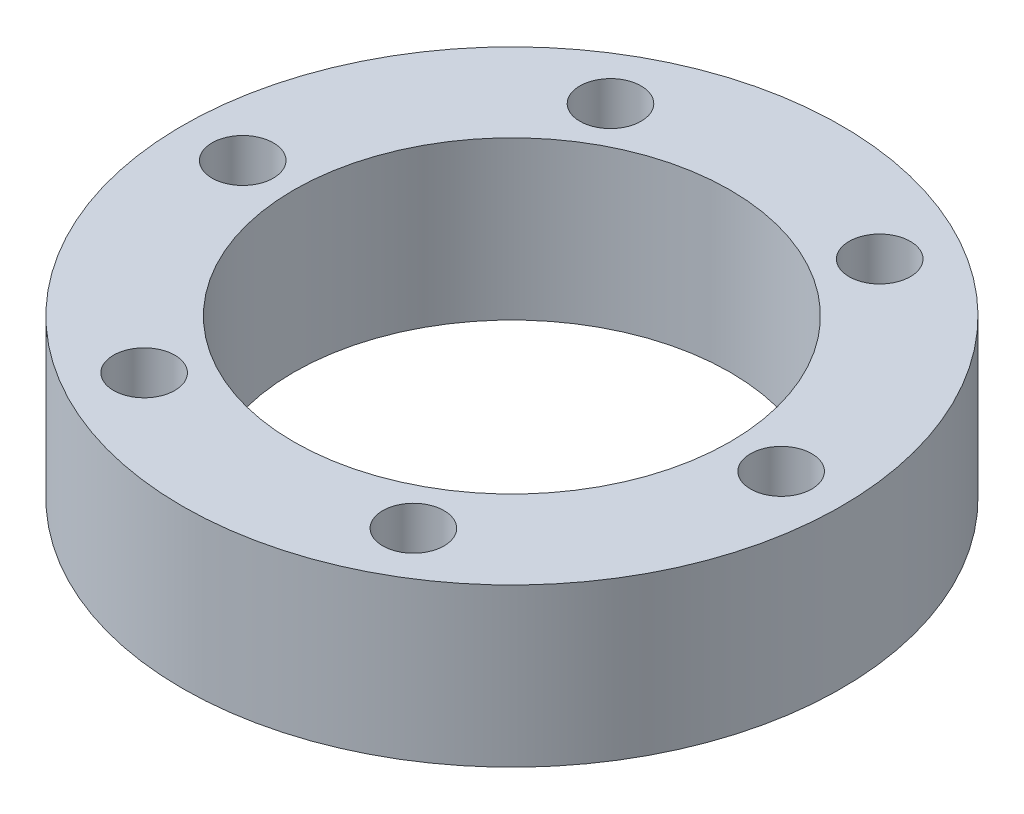
SolidWorks part; units mm, degrees
material "1.0036 (S235JRG1)"
ref_plane "Front Plane" through (0, 0, 0) normal (0, 0, 1) x (1, 0, 0)
ref_plane "Top Plane" through (0, 0, 0) normal (0, 1, 0) x (1, 0, 0)
ref_plane "Right Plane" through (0, 0, 0) normal (1, 0, 0) x (0, 0, -1)
sketch "Sketch1" plane through (0, 0, 0) normal (0, 1, 0) x (1, 0, 0)
  circle A0 centre (0, 0) radius 35.5
  circle A1 centre (0, 0) radius 23.5
  dimension "D1" = 47
  dimension "D2" = 12
extrude "Boss-Extrude1" add sketch "Sketch1" along normal blind 17
sketch "Sketch2" plane through (0, 17, 0) normal (0, 1, 0) x (1, 0, 0)
  point P0 (-29, 0)
  dimension "D1" = 29
hole_wizard "M6 Clearance Hole1" positions "3DSketch1" profile "Sketch4" hole size "M6" standard "ISO" end condition up to next
sketch3d "3DSketch1"
  point P0 (-29, 17, 0)
sketch "Sketch4" plane through (-29, 17, 0) normal (1, 0, 0) x (0, 0, 1)
  line L0 (0, 0) -> (0, 17)
  line L1 (0, 17) -> (3.3, 17)
  line L2 (3.3, 17) -> (3.3, 0)
  line L5 (3.3, 0) -> (0, 0)
  line L11 (0, -6.35) -> (0, 107.95) construction
  dimension "Thru Hole Dia." = 6.6
  dimension "Thru Hole Depth" = 17
pattern_circular "CirPattern1" count 6 over 360 about axis through (0, 0, 0) along (0, 1, 0) of "M6 Clearance Hole1"
